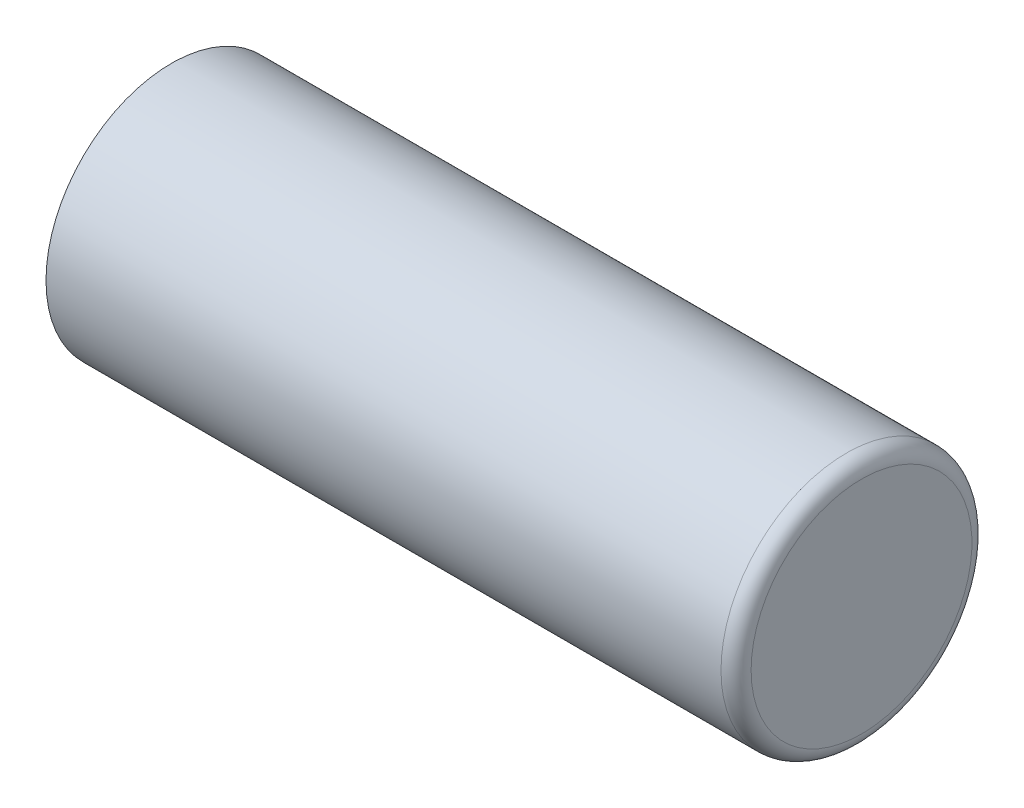
SolidWorks part; units mm, degrees
ref_plane "Front Plane" through (0, 0, 0) normal (0, 0, 1) x (1, 0, 0)
ref_plane "Top Plane" through (0, 0, 0) normal (0, 1, 0) x (1, 0, 0)
ref_plane "Right Plane" through (0, 0, 0) normal (1, 0, 0) x (0, 0, -1)
sketch "Sketch1" plane through (0, 0, 0) normal (0, 1, 0) x (1, 0, 0)
  line L0 (0, 0) -> (3.175, 0)
  line L1 (3.175, 0) -> (3.175, 11.176)
  line L2 (1.651, 12.7) -> (-66.675, 12.7)
  line L3 (-66.675, 12.7) -> (-66.675, 11.1125)
  line L4 (-66.675, 11.1125) -> (-65.0748, 11.1125)
  line L5 (-65.0748, 11.1125) -> (-65.0748, 9.525)
  line L6 (-65.0748, 9.525) -> (-1.524, 9.525)
  line L7 (0, 8.001) -> (0, 0)
  arc A0 (3.175, 11.176) -> (1.651, 12.7) centre (1.651, 11.176) ccw
  arc A1 (-1.524, 9.525) -> (0, 8.001) centre (-1.524, 8.001) cw
  point P11 (3.175, 12.7)
  dimension "D8" = 1.524
  dimension "D1" = 69.85
  dimension "D2" = 1.6002
  dimension "D3" = 9.525
  dimension "D4" = 11.1125
  dimension "D5" = 12.7
  dimension "D6" = 3.175
  dimension "D7" = 3.175
revolve "Revolve1" add sketch "Sketch1" angle 360 about L0
